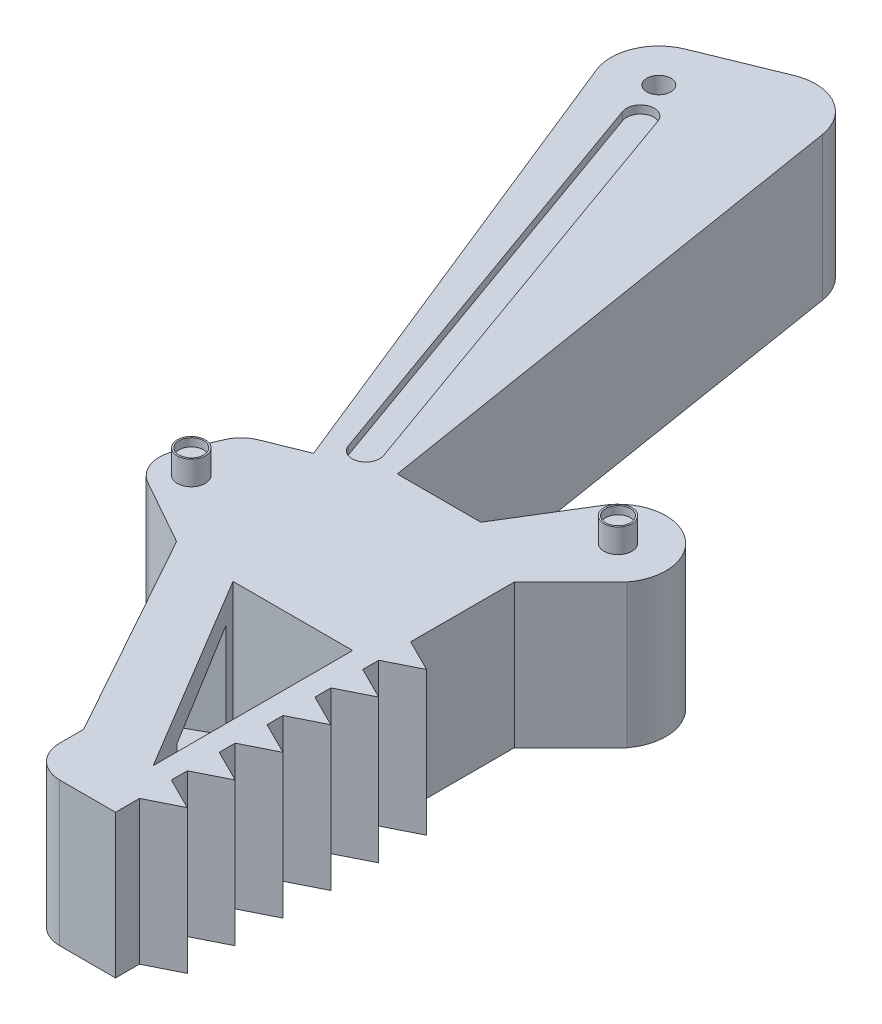
SolidWorks part; units mm, degrees
ref_plane "Front Plane" through (0, 0, 0) normal (0, 0, 1) x (1, 0, 0)
ref_plane "Top Plane" through (0, 0, 0) normal (0, 1, 0) x (1, 0, 0)
ref_plane "Right Plane" through (0, 0, 0) normal (1, 0, 0) x (0, 0, -1)
sketch "Sketch1" plane through (0, 0, 0) normal (0, 1, 0) x (1, 0, 0)
  line L0 (0, 0) -> (-66.3807, 0) construction
  line L1 (-19.8168, -74.0124) -> (-45.9537, -9.075)
  line L2 (-45.9537, -9.075) -> (-23.7356, 0)
  line L3 (-23.7356, 0) -> (-12.3325, -71)
  line L4 (-12.3325, -71) -> (-19.8168, -74.0124)
  line L5 (-12.3325, -71) -> (-26.2476, -76.6008)
  line L6 (-26.2476, -76.6008) -> (-30.167, -85.8007)
  line L7 (-30.167, -85.8007) -> (-18.8315, -92.1652)
  line L8 (-18.8315, -92.1652) -> (-4.2623, -118.3899)
  line L9 (-4.2623, -118.3899) -> (-4.2623, -125.3899)
  line L10 (-4.2623, -125.3899) -> (6.7377, -125.3899)
  line L11 (6.7377, -125.3899) -> (6.7377, -75.3899)
  line L12 (6.7377, -75.3899) -> (13.8088, -68.3188)
  line L13 (-12.3325, -71) -> (-1.849, -71)
  line L14 (-1.849, -71) -> (4.259, -61.0524)
  arc A0 (4.259, -61.0524) -> (13.8088, -68.3188) centre (9.0339, -64.6856) cw
  dimension "D12" = 6
  dimension "D1" = 70
  dimension "D2" = 71
  dimension "D3" = 24
  dimension "D4" = 15
  dimension "D5" = 10
  dimension "D6" = 13
  dimension "D7" = 30
  dimension "D8" = 7
  dimension "D9" = 11
  dimension "D10" = 50
  dimension "D11" = 10
  dimension "D13" = 10.4834
extrude "Boss-Extrude1" add sketch "Sketch1" along normal mid plane 18 contours A0 L14 L13 L4 L5 L6 L7 L8 L9 L10 L11 L12 | L4 L3 L2 L1
fillet "Fillet1" radius 6 2 edges at (-45.9537, 0, 9.075) (-23.7356, 0, 0)
fillet "Fillet2" radius 4 3 edges at (-4.2623, 0, 125.3899) (-30.167, 0, 85.8007) (-26.2476, 0, 76.6008)
sketch "Sketch2" plane through (0, 9, 0) normal (0, 1, 0) x (1, 0, 0)
  line L0 (6.7377, -118.3899) -> (6.7377, -122.3899)
  line L1 (6.7377, -125.3899) -> (6.7377, -75.3899) construction
  line L2 (6.7377, -120.3899) -> (10.7377, -120.3899) construction
  line L3 (6.7377, -118.3899) -> (10.7377, -120.3899)
  line L4 (10.7377, -120.3899) -> (6.7377, -122.3899)
  point P9 (6.7377, -120.3899)
  dimension "D1" = 5
  dimension "D2" = 4
  dimension "D3" = 4
extrude "Boss-Extrude2" add sketch "Sketch2" against normal blind 18
pattern_linear "LPattern1" count 6 spacing 6 along (0, 0, -1) of "Boss-Extrude2"
sketch "Sketch3" plane through (0, 9, 0) normal (0, 1, 0) x (1, 0, 0)
  line L0 (4.0395, -117.9626) -> (4.0395, -92.9626)
  line L1 (4.0395, -92.9626) -> (-10.9605, -92.9626)
  line L2 (-10.9605, -92.9626) -> (4.0395, -117.9626)
  dimension "D1" = 25
  dimension "D2" = 15
extrude "Cut-Extrude1" cut sketch "Sketch3" against normal through all contours L1 L2 L0
sketch "Sketch4" plane through (-53.5169, 0, 29.7316) normal (-0.8742, 0, 0.4856) x (0.4856, 0, 0.8742)
  line L0 (78.4214, 6) -> (78.4214, -6)
  line L1 (78.4214, -6) -> (96.4214, -5.431)
  line L2 (96.4214, -5.431) -> (96.4214, 5.431)
  line L3 (96.4214, 5.431) -> (78.4214, 6)
  line L4 (71.4214, 9) -> (71.4214, -9) construction
  line L5 (71.4214, 9) -> (101.4214, 9) construction
  line L6 (101.4214, 9) -> (101.4214, -9) construction
  point P6 (71.4214, 0)
  point P7 (78.4214, 0)
  point P8 (96.4214, 0)
  dimension "D1" = 3
  dimension "D2" = 5
  dimension "D3" = 7
extrude "Cut-Extrude2" cut sketch "Sketch4" against normal blind 8
sketch "Sketch5" plane through (0, 9, 0) normal (0, 1, 0) x (1, 0, 0)
  circle A0 centre (-38.1588, -12.3724) radius 1.5
  dimension "D1" = 3
extrude "Cut-Extrude3" cut sketch "Sketch5" against normal through all
sketch "Sketch6" plane through (0, 9, 0) normal (0, 1, 0) x (1, 0, 0)
  circle A0 centre (-25.0813, -84.0688) radius 1.75
  circle A1 centre (9.0339, -64.6856) radius 1.75
  dimension "D1" = 3.5
extrude "Boss-Extrude3" add sketch "Sketch6" along normal blind 3
sketch "Sketch7" plane through (0, 12, 0) normal (0, 1, 0) x (1, 0, 0)
  circle A2 centre (-25.0813, -84.0688) radius 1.55
  circle A3 centre (-25.0813, -84.0688) radius 1.55
  dimension "D1" = 0.2
extrude "Cut-Extrude4" cut sketch "Sketch7" against normal blind 1
sketch "Sketch8" plane through (0, 12, 0) normal (0, 1, 0) x (1, 0, 0)
  circle A2 centre (9.0339, -64.6856) radius 1.55
  circle A3 centre (9.0339, -64.6856) radius 1.55
  dimension "D1" = 0.2
extrude "Cut-Extrude5" cut sketch "Sketch8" against normal blind 1
sketch "Sketch9" plane through (0, 9, 0) normal (0, 1, 0) x (1, 0, 0)
  line L0 (-35.938, -16.9091) -> (-16.8123, -70.4479) construction
  line L1 (-34.3068, -16.3263) -> (-15.1811, -69.8652)
  line L2 (-37.5693, -17.4918) -> (-18.4436, -71.0306)
  arc A0 (-34.3068, -16.3263) -> (-37.5693, -17.4918) centre (-35.938, -16.9091) ccw
  arc A1 (-18.4436, -71.0306) -> (-15.1811, -69.8652) centre (-16.8123, -70.4479) ccw
  point P2 (-26.3752, -43.6785)
extrude "Cut-Extrude7" cut sketch "Sketch9" against normal blind 1
mirror "Mirror1" about plane through (0, 0, 0) normal (0, 1, 0) of "Boss-Extrude3", "Cut-Extrude4", "Cut-Extrude5", "Cut-Extrude7"
